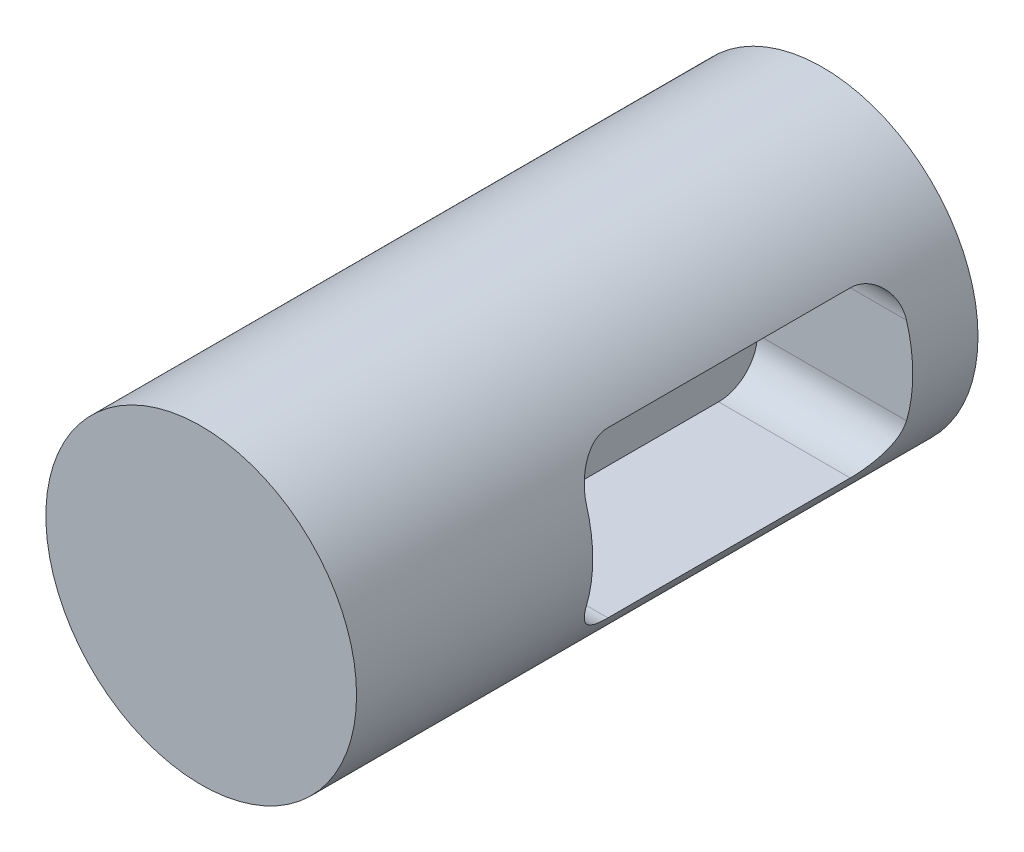
SolidWorks part; units mm, degrees
material "6061-T6 (SS)"
ref_plane "Front Plane" through (0, 0, 0) normal (0, 0, 1) x (1, 0, 0)
ref_plane "Top Plane" through (0, 0, 0) normal (0, 1, 0) x (1, 0, 0)
ref_plane "Right Plane" through (0, 0, 0) normal (1, 0, 0) x (0, 0, -1)
sketch "Sketch1" plane through (0, 0, 0) normal (0, 0, 1) x (1, 0, 0)
  circle A0 centre (0, 0) radius 6.35
  dimension "D1" = 12.7
extrude "Boss-Extrude1" add sketch "Sketch1" along normal blind 25.4
sketch "Sketch2" plane through (0, 0, 25.4) normal (0, 0, 1) x (1, 0, 0)
  line L0 (0, 0) -> (6.35, 0) construction
  circle A0 centre (0, 0) radius 6.35 construction
ref_plane "Plane1" through (6.35, 0, 0) normal (1, 0, 0) x (0, 0, -1)
sketch "Sketch4" plane through (6.35, 0, 0) normal (1, 0, 0) x (0, 0, -1)
  line L2 (-9.2075, 0) -> (-25.4, 0) construction
  line L3 (-25.4, 6.35) -> (-25.4, -6.35) construction
  line L5 (-15.748, -3.3655) -> (-2.667, -3.3655)
  line L6 (-15.748, -3.3655) -> (-15.748, 3.3655)
  line L7 (-15.748, 3.3655) -> (-2.667, 3.3655)
  line L8 (-2.667, -3.3655) -> (-2.667, 3.3655)
  line L9 (-15.748, -3.3655) -> (-2.667, 3.3655) construction
  line L10 (-15.748, 3.3655) -> (-2.667, -3.3655) construction
  dimension "D1" = 13.081
  dimension "D2" = 6.731
  dimension "D3" = 9.652
extrude "Cut-Extrude1" cut sketch "Sketch4" against normal blind 6.35
fillet "Fillet1" radius 1.5875 4 edges at (2.6924, 3.3655, 15.748) (2.6924, -3.3655, 15.748) (2.6924, 3.3655, 2.667) (2.6924, -3.3655, 2.667)
